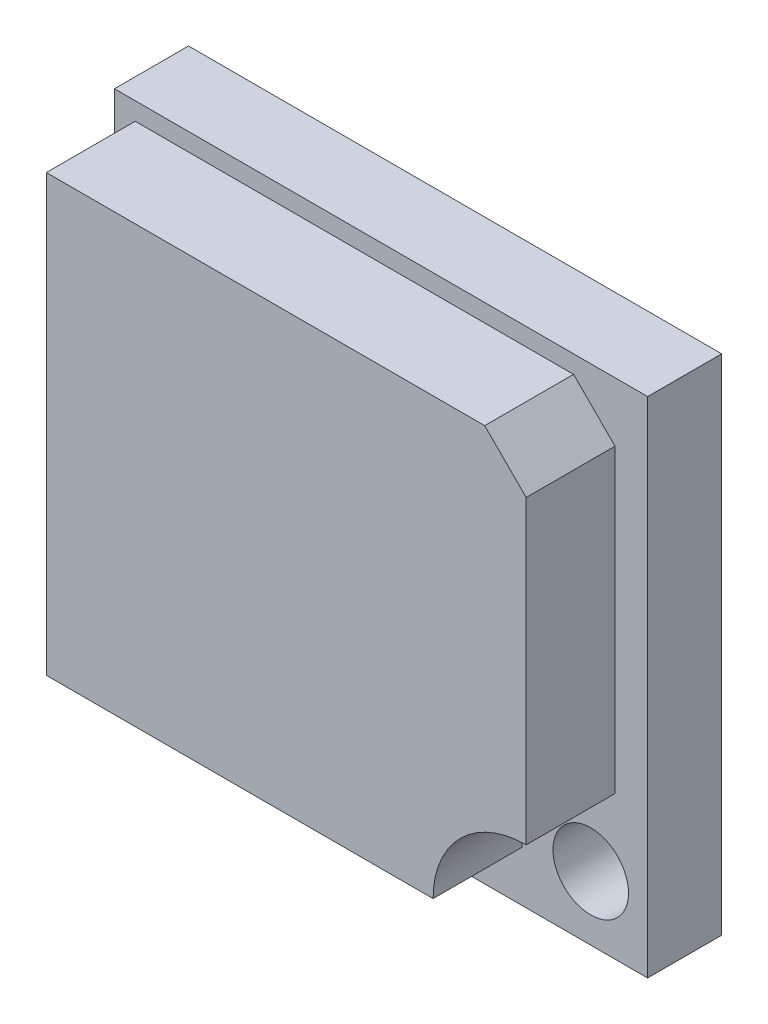
SolidWorks part; units mm, degrees
ref_plane "Front" through (0, 0, 0) normal (0, 0, 1) x (1, 0, 0)
ref_plane "Top" through (0, 0, 0) normal (0, 1, 0) x (1, 0, 0)
ref_plane "Right" through (0, 0, 0) normal (1, 0, 0) x (0, 0, -1)
sketch "Skizze1" plane through (0, 0, 0) normal (0, 0, 1) x (1, 0, 0)
  line L0 (0, 16.598) -> (0, 12.022) construction
  line L1 (0, 0) -> (18, 0)
  line L2 (0, 0) -> (0, 17)
  line L3 (0, 17) -> (18, 17)
  line L4 (18, 0) -> (18, 17)
  line L5 (18, 1.5) -> (18, 46.9) construction
  line L7 (23, 17) -> (18, 17) construction
extrude "Aufsatz-Linear austragen1" add sketch "Skizze1" along normal blind 2.5
sketch "Skizze2" plane through (0, 0, 2.5) normal (0, 0, 1) x (1, 0, 0)
  line L0 (0.7, 16.4) -> (0.7, 1.7)
  line L1 (0.7, 1.7) -> (13.7571, 1.7)
  line L5 (16.9, 4.8429) -> (16.9, 15)
  line L6 (16.9, 15) -> (15.5, 16.4)
  line L7 (15.5, 16.4) -> (0.7, 16.4)
  line L8 (0.6, 1.6) -> (0.6, 16.5) construction
  line L9 (0.6, 16.5) -> (7.33, 16.5) construction
  line L10 (7.33, 1.6) -> (0.6, 1.6) construction
  line L11 (17, 4.1) -> (17, 14) construction
  arc A0 (13.7571, 1.7) -> (16.9, 4.8429) centre (16.9, 1.7) cw
  dimension "D1" = 135
  dimension "D2" = 0.1
  dimension "D3" = 0.1
  dimension "D4" = 0.1
  dimension "D5" = 0.1
extrude "Aufsatz-Linear austragen2" add sketch "Skizze2" along normal blind 3
sketch "Skizze3" plane through (0, 0, 2.5) normal (0, 0, 1) x (1, 0, 0)
  circle A0 centre (16.079, 2.1576) radius 1.275
  dimension "D1" = 2.55
extrude "Schnitt-Linear austragen1" cut sketch "Skizze3" against normal through all
